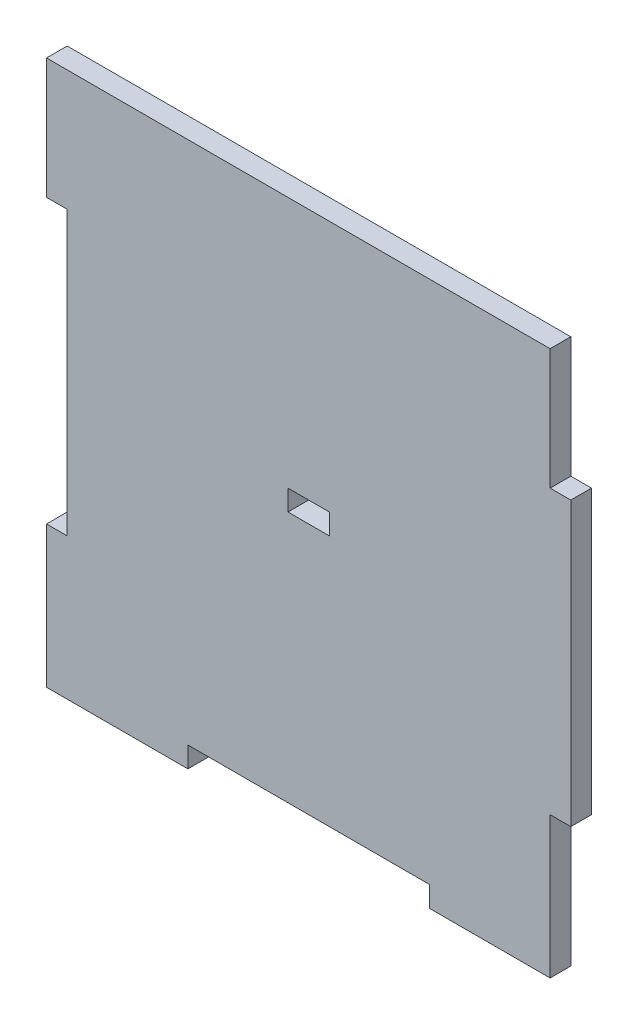
SolidWorks part; units mm, degrees
ref_plane "Front Plane" through (0, 0, 0) normal (0, 0, 1) x (1, 0, 0)
ref_plane "Top Plane" through (0, 0, 0) normal (0, 1, 0) x (1, 0, 0)
ref_plane "Right Plane" through (0, 0, 0) normal (1, 0, 0) x (0, 0, -1)
sketch "Sketch1" plane through (0, 0, 0) normal (0, 0, 1) x (1, 0, 0)
  line L0 (0, 35) -> (0, -38) construction
  line L5 (-35, 38) -> (-17.5, 38)
  line L6 (-35, 20.5) -> (-35, -20.5)
  line L7 (-17.5, -38) -> (17.5, -38)
  line L24 (35, 38) -> (35, 20.5)
  line L25 (-35, 38) -> (35, -38) construction
  line L26 (-35, -38) -> (35, 38) construction
  line L27 (-35, 0) -> (35, 0) construction
  line L31 (-35, -20.5) -> (-38, -20.5)
  line L32 (-35, 20.5) -> (-38, 20.5)
  line L33 (-38, 20.5) -> (-38, 38)
  line L34 (-38, 38) -> (-35, 38)
  line L35 (-38, -20.5) -> (-38, -38)
  line L36 (-17.5, 38) -> (17.5, 38)
  line L37 (35, -38) -> (35, -41)
  line L38 (35, -20.5) -> (38, -20.5)
  line L39 (35, -41) -> (17.5, -41)
  line L40 (35, 20.5) -> (38, 20.5)
  line L41 (17.5, -41) -> (17.5, -38)
  line L42 (-17.5, -38) -> (-17.5, -41)
  line L43 (38, 20.5) -> (38, -20.5)
  line L45 (-35, -41) -> (-17.5, -41)
  line L46 (17.5, 38) -> (35, 38)
  line L47 (35, -20.5) -> (35, -38)
  line L48 (-38, -38) -> (-38, -41)
  line L49 (-38, -41) -> (-35, -41)
  point P0 (0, 0)
  dimension "D1" = 76
  dimension "D2" = 70
  dimension "D3" = 17.5
  dimension "D4" = 17.5
  dimension "D5" = 3
  dimension "D6" = 3
  dimension "D7" = 3
extrude "Boss-Extrude1" add sketch "Sketch1" along normal blind 3
sketch "Sketch2" plane through (0, 0, 3) normal (0, 0, 1) x (1, 0, 0)
  line L1 (-3, -1.5) -> (3, -1.5)
  line L2 (-3, -1.5) -> (-3, 1.5)
  line L3 (-3, 1.5) -> (3, 1.5)
  line L4 (3, -1.5) -> (3, 1.5)
  line L5 (-3, -1.5) -> (3, 1.5) construction
  line L6 (-3, 1.5) -> (3, -1.5) construction
  point P0 (0, 0)
  dimension "D1" = 6
  dimension "D2" = 3
extrude "Cut-Extrude1" cut sketch "Sketch2" against normal blind 3
